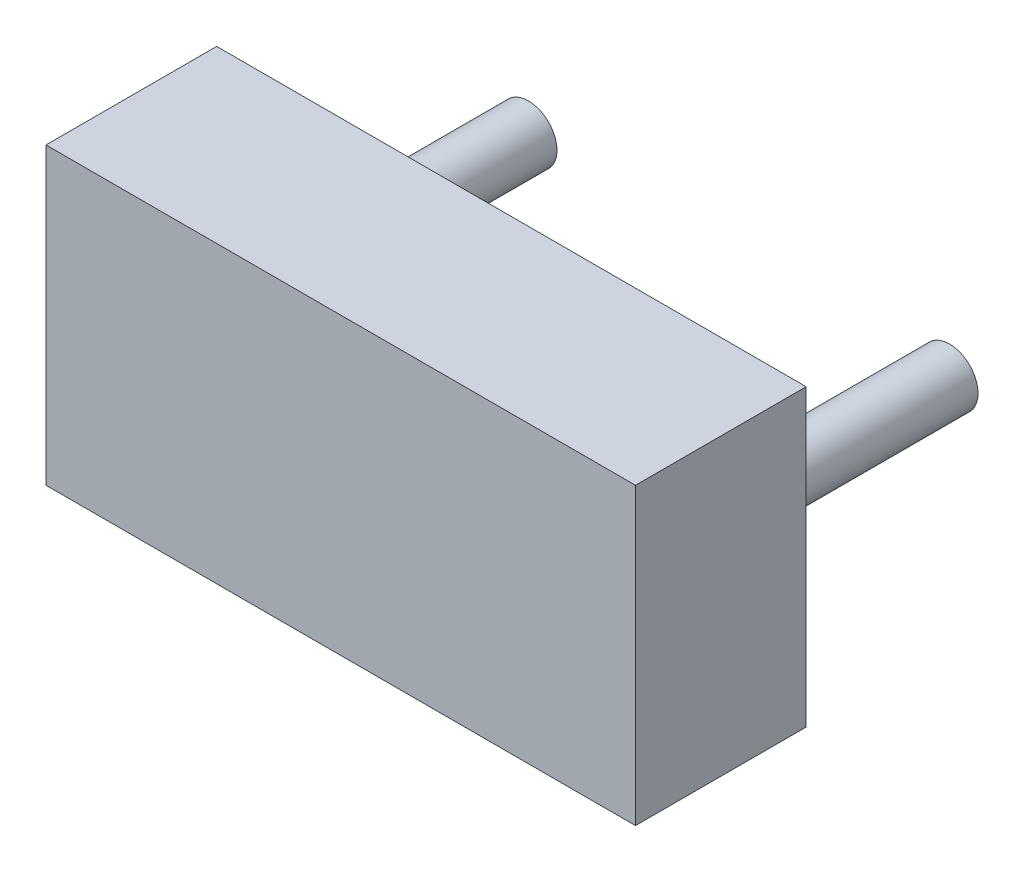
SolidWorks part; units mm, degrees
ref_plane "Front Plane" through (0, 0, 0) normal (0, 0, 1) x (1, 0, 0)
ref_plane "Top Plane" through (0, 0, 0) normal (0, 1, 0) x (1, 0, 0)
ref_plane "Right Plane" through (0, 0, 0) normal (1, 0, 0) x (0, 0, -1)
sketch "Sketch1" plane through (0, 0, 0) normal (0, 0, 1) x (1, 0, 0)
  line L0 (2.59, 1.295) -> (-2.59, 1.295)
  line L1 (-2.59, 1.295) -> (-2.59, -1.295)
  line L2 (-2.59, -1.295) -> (2.59, -1.295)
  line L3 (2.59, -1.295) -> (2.59, 1.295)
extrude "Component_Outline" add sketch "Sketch1" along normal blind 1.5 separate body
sketch "Sketch2" plane through (0, 0, 0) normal (0, 0, 1) x (1, 0, 0)
  circle A0 centre (-1.85, 0) radius 0.25
extrude "1" add sketch "Sketch2" against normal blind 2 separate body
sketch "Sketch3" plane through (0, 0, 0) normal (0, 0, 1) x (1, 0, 0)
  circle A0 centre (1.85, 0) radius 0.25
extrude "2" add sketch "Sketch3" against normal blind 2 separate body
sketch3d "3DSketch1"
  line L0 (0, 0, 0) -> (1, 0, 0)
  line L1 (0, 0, 0) -> (0, 1, 0)
  line L2 (0, 0, 0) -> (0, 0, 1)
  point P0 (0, 0, 0)
